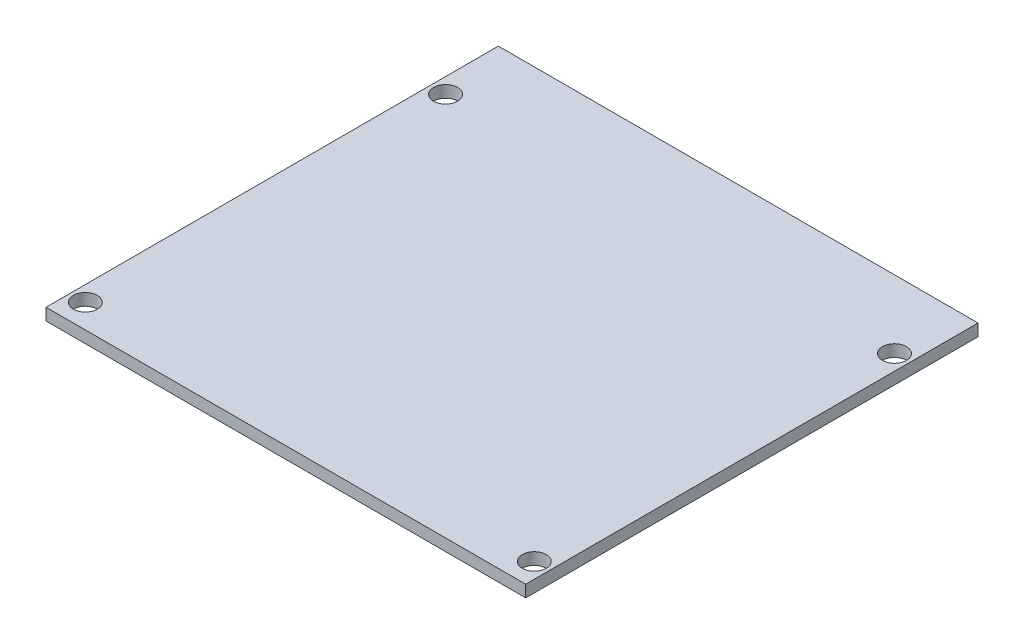
SolidWorks part; units mm, degrees
ref_plane "Front Plane" through (0, 0, 0) normal (0, 0, 1) x (1, 0, 0)
ref_plane "Top Plane" through (0, 0, 0) normal (0, 1, 0) x (1, 0, 0)
ref_plane "Right Plane" through (0, 0, 0) normal (1, 0, 0) x (0, 0, -1)
sketch "Sketch2" plane through (0, 0, 0) normal (0, 1, 0) x (1, 0, 0)
  line L1 (-32.025, -30.2) -> (32.025, -30.2)
  line L2 (-32.025, -30.2) -> (-32.025, 30.2)
  line L3 (-32.025, 30.2) -> (32.025, 30.2)
  line L4 (32.025, -30.2) -> (32.025, 30.2)
  line L5 (-32.025, -30.2) -> (32.025, 30.2) construction
  line L6 (-32.025, 30.2) -> (32.025, -30.2) construction
  point P0 (0, 0)
  dimension "D1" = 64.05
  dimension "D2" = 60.4
sketch "Sketch3" plane through (0, 0, 0) normal (0, 1, 0) x (1, 0, 0)
  line L1 (-29.972, -27) -> (29.972, -27) construction
  line L2 (-29.972, -27) -> (-29.972, 21.1) construction
  line L3 (-29.972, 21.1) -> (29.972, 21.1) construction
  line L4 (29.972, -27) -> (29.972, 21.1) construction
  line L5 (-29.972, -27) -> (29.972, 21.1) construction
  line L6 (-29.972, 21.1) -> (29.972, -27) construction
  line L8 (-32.025, -30.2) -> (32.025, -30.2) construction
  line L9 (-32.025, 30.2) -> (32.025, 30.2) construction
  circle A0 centre (-29.972, 21.1) radius 1.6
  circle A1 centre (29.972, 21.1) radius 1.6
  circle A2 centre (29.972, -27) radius 1.6
  circle A3 centre (-29.972, -27) radius 1.6
  point P0 (0, -2.95)
  point P12 (0, 0)
  dimension "D4" = 3.2
  dimension "D2" = 59.944
  dimension "D1" = 3.2
  dimension "D3" = 9.1
extrude "Boss-Extrude1" add sketch "Sketch2" along normal mid plane 1.5875
extrude "Cut-Extrude1" cut sketch "Sketch3" against normal through all both and the other way through all
equation "\"D1@Sketch2\"=64.05mm"
equation "\"D2@Sketch2\"=60.4mm"
equation "\"D2@Sketch3\"=59.944mm"
equation "\"D1@Sketch3\"=3.2mm"
equation "\"D3@Sketch3\"=9.1mm"
equation "\"D4@Sketch3\"=3.2mm"
